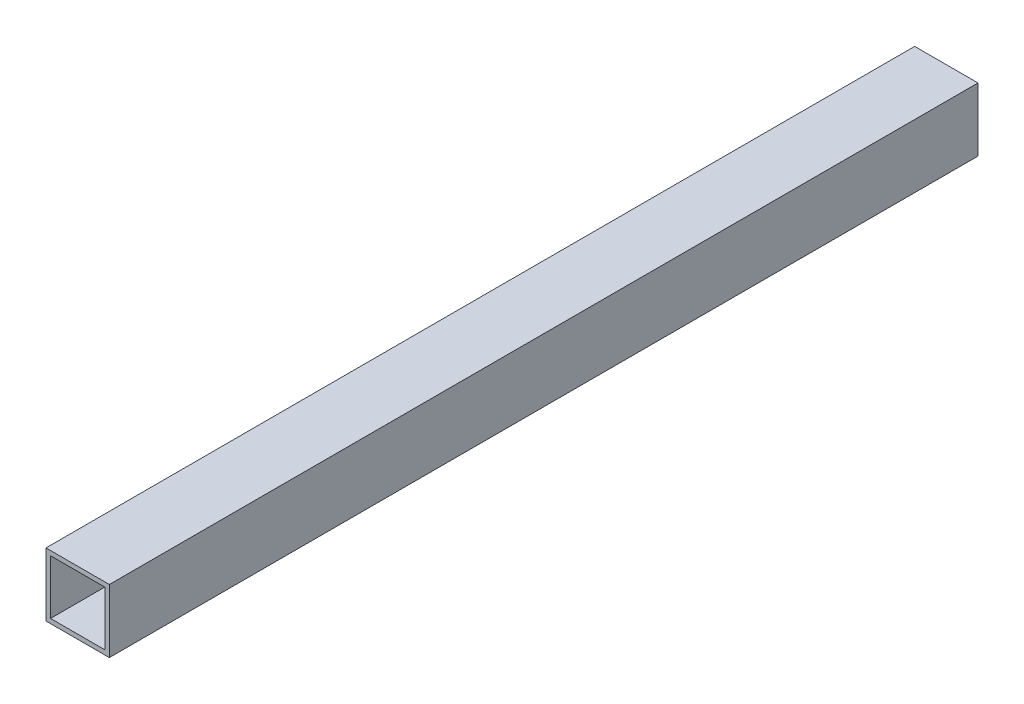
SolidWorks part; units mm, degrees
material "6063-T6"
ref_plane "Front Plane" through (0, 0, 0) normal (0, 0, 1) x (1, 0, 0)
ref_plane "Top Plane" through (0, 0, 0) normal (0, 1, 0) x (1, 0, 0)
ref_plane "Right Plane" through (0, 0, 0) normal (1, 0, 0) x (0, 0, -1)
sketch "Sketch1" plane through (0, 0, 0) normal (0, 0, 1) x (1, 0, 0)
  line L0 (3.175, 3.175) -> (3.175, 41.275)
  line L1 (0, 0) -> (44.45, 0)
  line L2 (0, 0) -> (0, 44.45)
  line L3 (0, 44.45) -> (44.45, 44.45)
  line L4 (44.45, 0) -> (44.45, 44.45)
  line L5 (3.175, 41.275) -> (41.275, 41.275)
  line L6 (41.275, 3.175) -> (41.275, 41.275)
  line L7 (3.175, 3.175) -> (41.275, 3.175)
  dimension "D2" = 44.45
  dimension "D1" = 3.175
extrude "Boss-Extrude1" add sketch "Sketch1" along normal blind 609.6
